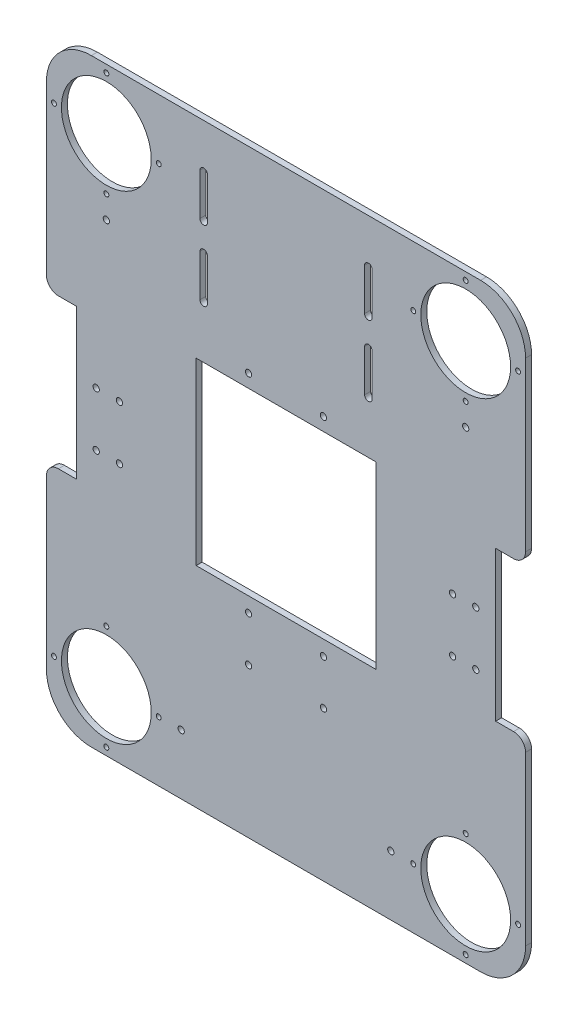
SolidWorks part; units mm, degrees
ref_plane "前视基准面" through (0, 0, 0) normal (0, 0, 1) x (1, 0, 0)
ref_plane "上视基准面" through (0, 0, 0) normal (0, 1, 0) x (1, 0, 0)
ref_plane "右视基准面" through (0, 0, 0) normal (1, 0, 0) x (0, 0, -1)
sketch "草图1" plane through (0, 0, 0) normal (0, 0, 1) x (1, 0, 0)
  line L0 (-140, 50) -> (-140, -50)
  line L5 (-160, 200) -> (160, -200) construction
  line L6 (-160, -200) -> (160, 200) construction
  line L7 (-60, 60) -> (60, 60)
  line L8 (-60, 60) -> (-60, -60)
  line L9 (-60, -60) -> (60, -60)
  line L10 (60, 60) -> (60, -60)
  line L11 (-60, 60) -> (60, -60) construction
  line L12 (-60, -60) -> (60, 60) construction
  line L13 (140, 50) -> (140, -50)
  line L14 (-160, 170) -> (-160, 58)
  line L15 (-160, -58) -> (-160, -170)
  line L16 (160, -170) -> (160, -58)
  line L17 (160, 58) -> (160, 170)
  line L18 (-140, 50) -> (-152, 50)
  line L19 (-140, -50) -> (-152, -50)
  line L20 (140, 50) -> (152, 50)
  line L21 (140, -50) -> (152, -50)
  line L22 (-103, 19.3) -> (-140, 19.3) construction
  line L23 (-103, 19.3) -> (-103, -36.7) construction
  line L24 (-103, -36.7) -> (-140, -36.7) construction
  line L25 (-103, -26.7) -> (-109, -26.7) construction
  line L26 (-109, 9.3) -> (-129, 9.3) construction
  line L27 (-103, 9.3) -> (-109, 9.3) construction
  line L28 (-109, 6.55) -> (-129, 6.55) construction
  line L29 (-109, 12.05) -> (-129, 12.05) construction
  line L30 (-109, -26.7) -> (-129, -26.7) construction
  line L33 (-109, -29.45) -> (-129, -29.45) construction
  line L36 (-109, -23.95) -> (-129, -23.95) construction
  line L37 (140, 19.3) -> (103, 19.3) construction
  line L40 (103, 19.3) -> (103, -36.7) construction
  line L43 (103, -36.7) -> (140, -36.7) construction
  line L44 (109, 9.3) -> (129, 9.3) construction
  line L45 (103, 9.3) -> (109, 9.3) construction
  line L46 (109, 12.05) -> (129, 12.05) construction
  line L47 (109, 6.55) -> (129, 6.55) construction
  line L48 (109, -26.7) -> (129, -26.7) construction
  line L49 (109, -23.95) -> (129, -23.95) construction
  line L50 (109, -29.45) -> (129, -29.45) construction
  line L51 (0, -60) -> (0, -45) construction
  line L52 (0, 60) -> (0, 35) construction
  line L53 (160, 160) -> (120, 160) construction
  line L54 (60, 0) -> (35, 0) construction
  line L55 (-160, -160.002) -> (-120, -160.002) construction
  line L56 (-60, 0) -> (-35, 0) construction
  line L57 (160, -160.002) -> (120, -160.002) construction
  line L58 (35, 35) -> (35, -35) construction
  line L59 (-140, 19.3) -> (-100, 19.3) construction
  line L60 (-140, -8.7) -> (140, -8.7) construction
  line L61 (-100, 19.3) -> (-100, -115.7) construction
  line L62 (-100, -115.7) -> (-140, -115.7) construction
  line L63 (-140, -115.7) -> (-140, -50) construction
  line L64 (-130, 200) -> (130, 200)
  line L65 (-130, -200) -> (130, -200)
  line L67 (-35, -35) -> (-35, 35) construction
  line L68 (-35, 35) -> (35, 35) construction
  line L69 (-120, 160) -> (-85, 160) construction
  line L70 (-120, 160) -> (-120, 125) construction
  line L71 (120, 160) -> (155, 160) construction
  line L72 (120, 160) -> (85, 160) construction
  line L73 (0, -45) -> (20, -45) construction
  line L74 (0, -45) -> (-20, -45) construction
  line L75 (35, -35) -> (20, -35) construction
  line L76 (-120, -160.002) -> (-85, -160.002) construction
  line L78 (20, -35) -> (20, -45) construction
  line L83 (-55, 90) -> (55, 90) construction
  line L84 (-55, 90) -> (-55, 175) construction
  line L85 (-55, 175) -> (55, 175) construction
  line L86 (55, 175) -> (55, 90) construction
  line L87 (-55, 132.5) -> (-55, 142) construction
  line L88 (-55, 132.5) -> (-55, 123) construction
  line L89 (-55, 142) -> (-55, 170) construction
  line L90 (-55, 123) -> (-55, 95) construction
  line L91 (-55, 170) -> (-55, 142) construction
  line L92 (-52.5, 170) -> (-52.5, 142)
  line L93 (-57.5, 170) -> (-57.5, 142)
  line L94 (-55, 123) -> (-55, 95) construction
  line L95 (-52.5, 123) -> (-52.5, 95)
  line L96 (-57.5, 123) -> (-57.5, 95)
  line L97 (55, 132.5) -> (55, 142) construction
  line L98 (55, 132.5) -> (55, 123) construction
  line L99 (55, 142) -> (55, 170) construction
  line L100 (55, 123) -> (55, 95) construction
  line L101 (55, 170) -> (55, 142) construction
  line L102 (57.5, 170) -> (57.5, 142)
  line L103 (52.5, 170) -> (52.5, 142)
  line L104 (55, 123) -> (55, 95) construction
  line L105 (57.5, 123) -> (57.5, 95)
  line L106 (52.5, 123) -> (52.5, 95)
  line L107 (-20, -45) -> (-20, -35) construction
  line L108 (-20, -35) -> (-35, -35) construction
  line L109 (-120, 160) -> (-120, 110) construction
  line L110 (35, -60) -> (35, -110) construction
  line L111 (35, -110) -> (-35, -110) construction
  line L112 (-35, -110) -> (-35, -60) construction
  line L113 (120, 160) -> (120, 110) construction
  line L114 (-129, 9.3) -> (-126.75, 9.3) construction
  line L115 (120, -160.002) -> (70, -160.002) construction
  line L116 (-109, 9.3) -> (-111.25, 9.3) construction
  line L117 (129, 9.3) -> (126.75, 9.3) construction
  line L118 (109, 9.3) -> (111.25, 9.3) construction
  circle A8 centre (-120, 160) radius 30
  circle A9 centre (120, 160) radius 30
  circle A10 centre (-120, -160.002) radius 30
  circle A11 centre (120, -160.002) radius 30
  circle A12 centre (-120, 195) radius 1.5
  circle A13 centre (-155, 160) radius 1.5
  circle A14 centre (-120, 125) radius 1.5
  circle A15 centre (-85, 160) radius 1.5
  circle A16 centre (120, 195) radius 1.5
  circle A17 centre (155, 160) radius 1.5
  circle A18 centre (85, 160) radius 1.5
  circle A19 centre (120, 125) radius 1.5
  circle A20 centre (-155, -160.002) radius 1.5
  circle A21 centre (-120, -195.002) radius 1.5
  circle A22 centre (-120, -125.002) radius 1.5
  circle A23 centre (-85, -160.002) radius 1.5
  circle A24 centre (155, -160.002) radius 1.5
  circle A25 centre (120, -195.002) radius 1.5
  circle A27 centre (120, -125.002) radius 1.5
  arc A28 (-52.5, 170) -> (-57.5, 170) centre (-55, 170) ccw
  arc A29 (-57.5, 142) -> (-52.5, 142) centre (-55, 142) ccw
  arc A30 (-52.5, 123) -> (-57.5, 123) centre (-55, 123) ccw
  arc A31 (-57.5, 95) -> (-52.5, 95) centre (-55, 95) ccw
  arc A32 (57.5, 170) -> (52.5, 170) centre (55, 170) ccw
  arc A33 (52.5, 142) -> (57.5, 142) centre (55, 142) ccw
  arc A34 (57.5, 123) -> (52.5, 123) centre (55, 123) ccw
  arc A35 (52.5, 95) -> (57.5, 95) centre (55, 95) ccw
  arc A36 (-109, 6.55) -> (-109, 12.05) centre (-109, 9.3) ccw construction
  arc A37 (-129, 12.05) -> (-129, 6.55) centre (-129, 9.3) ccw construction
  arc A38 (-109, -29.45) -> (-109, -23.95) centre (-109, -26.7) ccw construction
  arc A39 (-129, -23.95) -> (-129, -29.45) centre (-129, -26.7) ccw construction
  arc A40 (109, 12.05) -> (109, 6.55) centre (109, 9.3) ccw construction
  arc A41 (129, 6.55) -> (129, 12.05) centre (129, 9.3) ccw construction
  arc A42 (109, -23.95) -> (109, -29.45) centre (109, -26.7) ccw construction
  arc A43 (129, -29.45) -> (129, -23.95) centre (129, -26.7) ccw construction
  circle A44 centre (85, -160.002) radius 1.5
  arc A45 (160, -170) -> (130, -200) centre (130, -170) cw
  arc A46 (-130, -200) -> (-160, -170) centre (-130, -170) cw
  arc A47 (160, 170) -> (130, 200) centre (130, 170) ccw
  arc A48 (-160, 170) -> (-130, 200) centre (-130, 170) cw
  arc A49 (152, -50) -> (160, -58) centre (152, -58) cw
  arc A50 (152, 50) -> (160, 58) centre (152, 58) ccw
  arc A51 (-160, -58) -> (-152, -50) centre (-152, -58) cw
  arc A52 (-152, 50) -> (-160, 58) centre (-152, 58) cw
  circle A53 centre (25, -100) radius 2
  circle A54 centre (25, -70) radius 2
  circle A55 centre (-25, -100) radius 2
  circle A56 centre (-25, -70) radius 2
  circle A57 centre (-25, 68.76) radius 2
  circle A58 centre (25, 68.76) radius 2
  circle A59 centre (-120, 110) radius 2
  circle A60 centre (120, 110) radius 2
  circle A61 centre (-70, -160.002) radius 2
  circle A62 centre (70, -160.002) radius 2
  circle A63 centre (-126.75, 9.3) radius 2
  circle A64 centre (-111.25, 9.3) radius 2
  circle A65 centre (-126.75, -26.7) radius 2
  circle A66 centre (-111.25, -26.7) radius 2
  circle A67 centre (111.25, 9.3) radius 2
  circle A68 centre (126.75, 9.3) radius 2
  circle A69 centre (111.25, -26.7) radius 2
  circle A70 centre (126.75, -26.7) radius 2
  point P0 (0, 0)
  point P6 (0, 0)
  point P11 (-119, 9.3)
  point P25 (119, 9.3)
  point P35 (-119, -26.7)
  point P53 (119, -26.7)
  point P125 (-55, 156)
  point P133 (-55, 109)
  point P140 (55, 156)
  point P148 (55, 109)
  point P156 (160, 50)
  point P159 (-160, -50)
  point P162 (-160, 50)
  dimension "D9" = 56
  dimension "D14" = 400
  dimension "D21" = 35
  dimension "D23" = 60
  dimension "D24" = 60
  dimension "D26" = 40
  dimension "D28" = 60
  dimension "D29" = 60
  dimension "D36" = 3
  dimension "D37" = 3
  dimension "D40" = 3
  dimension "D41" = 3
  dimension "D42" = 35
  dimension "D44" = 3
  dimension "D45" = 3
  dimension "D46" = 3
  dimension "D47" = 3
  dimension "D48" = 3
  dimension "D49" = 3
  dimension "D50" = 3
  dimension "D51" = 3
  dimension "D52" = 3
  dimension "D53" = 36
  dimension "D54" = 3
  dimension "D55" = 3
  dimension "D60" = 135
  dimension "D10" = 37
  dimension "D12" = 5.5
  dimension "D33" = 3
  dimension "D73" = 30
  dimension "D74" = 8
  dimension "D77" = 10
  dimension "D79" = 8.76
  dimension "D81" = 4
  dimension "D82" = 4
  dimension "D84" = 4
  dimension "D85" = 4
  dimension "D86" = 4
  dimension "D87" = 4
  dimension "D88" = 4
  dimension "D89" = 4
  dimension "D90" = 4
  dimension "D91" = 4
  dimension "D94" = 13.25
  dimension "D96" = 4
  dimension "D97" = 4
  dimension "D2" = 320
  dimension "D3" = 120
  dimension "D7" = 6
  dimension "D8" = 37
  dimension "D11" = 6
  dimension "D13" = 39.998
  dimension "D15" = 35
  dimension "D16" = 35
  dimension "D17" = 100
  dimension "D18" = 35
  dimension "D19" = 20
  dimension "D20" = 20
  dimension "D22" = 35
  dimension "D25" = 40
  dimension "D27" = 35
  dimension "D30" = 40
  dimension "D31" = 35
  dimension "D32" = 58.7
  dimension "D34" = 40
  dimension "D35" = 35
  dimension "D38" = 35
  dimension "D39" = 35
  dimension "D43" = 35
  dimension "D56" = 30
  dimension "D57" = 5
  dimension "D58" = 5
  dimension "D59" = 28
  dimension "D61" = 110
  dimension "D62" = 85
  dimension "D63" = 40
  dimension "D64" = 5
  dimension "D65" = 120
  dimension "D66" = 35
  dimension "D67" = 40
  dimension "D68" = 28
  dimension "D69" = 5
  dimension "D70" = 28
  dimension "D71" = 5
  dimension "D72" = 28
  dimension "D75" = 70
  dimension "D76" = 50
  dimension "D78" = 10
  dimension "D80" = 10
  dimension "D83" = 50
  dimension "D92" = 50
  dimension "D93" = 50
  dimension "D95" = 15.5
  dimension "D98" = 15.5
  dimension "D99" = 13.25
extrude "凸台-拉伸1" add sketch "草图1" along normal blind 4
hole_wizard "M4 螺纹孔1" positions "草图2" profile "草图3" tap size "M4" standard "GB" end condition through all
sketch "草图2" plane through (0, 0, 4) normal (0, 0, 1) x (1, 0, 0)
  point P0 (-120, 195)
  point P3 (-155, 160)
  point P6 (-85, 160)
  point P9 (-120, 125)
  point P12 (120, 195)
  point P15 (85, 160)
  point P18 (120, 125)
  point P21 (155, 160)
  point P24 (-120, -125.002)
  point P27 (-155, -160.002)
  point P30 (-85, -160.002)
  point P33 (-120, -195.002)
  point P36 (120, -125.002)
  point P39 (85, -160.002)
  point P42 (155, -160.002)
  point P45 (120, -195.002)
sketch "草图3" plane through (-120, 195, 4) normal (1, 0, 0) x (0, -1, 0)
  line L0 (0, 0) -> (0, 4)
  line L1 (0, 4) -> (1.65, 4)
  line L2 (1.65, 4) -> (1.65, 0)
  line L5 (1.65, 0) -> (0, 0)
  line L11 (0, -6.35) -> (0, 107.95) construction
  dimension "通孔螺纹孔钻头直径" = 3.3
  dimension "通孔螺纹孔钻头深度" = 4
cosmetic thread "孔螺蚊线1" parameters "D2"=4
cosmetic thread "孔螺蚊线2" parameters "D2"=4
cosmetic thread "孔螺蚊线3" parameters "D2"=4
cosmetic thread "孔螺蚊线4" parameters "D2"=4
cosmetic thread "孔螺蚊线5" parameters "D2"=4
cosmetic thread "孔螺蚊线6" parameters "D2"=4
cosmetic thread "孔螺蚊线7" parameters "D2"=4
cosmetic thread "孔螺蚊线8" parameters "D2"=4
cosmetic thread "孔螺蚊线9" parameters "D2"=4
cosmetic thread "孔螺蚊线10" parameters "D2"=4
cosmetic thread "孔螺蚊线11" parameters "D2"=4
cosmetic thread "孔螺蚊线12" parameters "D2"=4
cosmetic thread "孔螺蚊线13" parameters "D2"=4
cosmetic thread "孔螺蚊线14" parameters "D2"=4
cosmetic thread "孔螺蚊线15" parameters "D2"=4
cosmetic thread "孔螺蚊线16" parameters "D2"=4
hole_wizard "M5 螺纹孔1" positions "草图4" profile "草图5" tap size "M5" standard "GB" end condition through all
sketch "草图4" plane through (0, 0, 4) normal (0, 0, 1) x (1, 0, 0)
  point P0 (-120, 110)
  point P3 (-25, 68.76)
  point P6 (25, 68.76)
  point P9 (120, 110)
  point P12 (-25, -70)
  point P15 (25, -70)
  point P18 (25, -100)
  point P21 (-25, -100)
  point P24 (-70, -160.002)
  point P27 (70, -160.002)
  point P31 (-126.75, 9.3)
  point P34 (-111.25, 9.3)
  point P37 (-126.75, -26.7)
  point P40 (-111.25, -26.7)
  point P43 (111.25, 9.3)
  point P46 (126.75, 9.3)
  point P49 (111.25, -26.7)
  point P52 (126.75, -26.7)
sketch "草图5" plane through (-120, 110, 4) normal (1, 0, 0) x (0, -1, 0)
  line L0 (0, 0) -> (0, 4)
  line L1 (0, 4) -> (2.1, 4)
  line L2 (2.1, 4) -> (2.1, 0)
  line L5 (2.1, 0) -> (0, 0)
  line L11 (0, -6.35) -> (0, 107.95) construction
  dimension "通孔螺纹孔钻头直径" = 4.2
  dimension "通孔螺纹孔钻头深度" = 4
cosmetic thread "孔螺蚊线17" parameters "D2"=5
cosmetic thread "孔螺蚊线18" parameters "D2"=5
cosmetic thread "孔螺蚊线19" parameters "D2"=5
cosmetic thread "孔螺蚊线20" parameters "D2"=5
cosmetic thread "孔螺蚊线21" parameters "D2"=5
cosmetic thread "孔螺蚊线22" parameters "D2"=5
cosmetic thread "孔螺蚊线23" parameters "D2"=5
cosmetic thread "孔螺蚊线24" parameters "D2"=5
cosmetic thread "孔螺蚊线25" parameters "D2"=5
cosmetic thread "孔螺蚊线26" parameters "D2"=5
cosmetic thread "孔螺蚊线27" parameters "D2"=5
cosmetic thread "孔螺蚊线28" parameters "D2"=5
cosmetic thread "孔螺蚊线29" parameters "D2"=5
cosmetic thread "孔螺蚊线30" parameters "D2"=5
cosmetic thread "孔螺蚊线31" parameters "D2"=5
cosmetic thread "孔螺蚊线32" parameters "D2"=5
cosmetic thread "孔螺蚊线33" parameters "D2"=5
cosmetic thread "孔螺蚊线34" parameters "D2"=5
